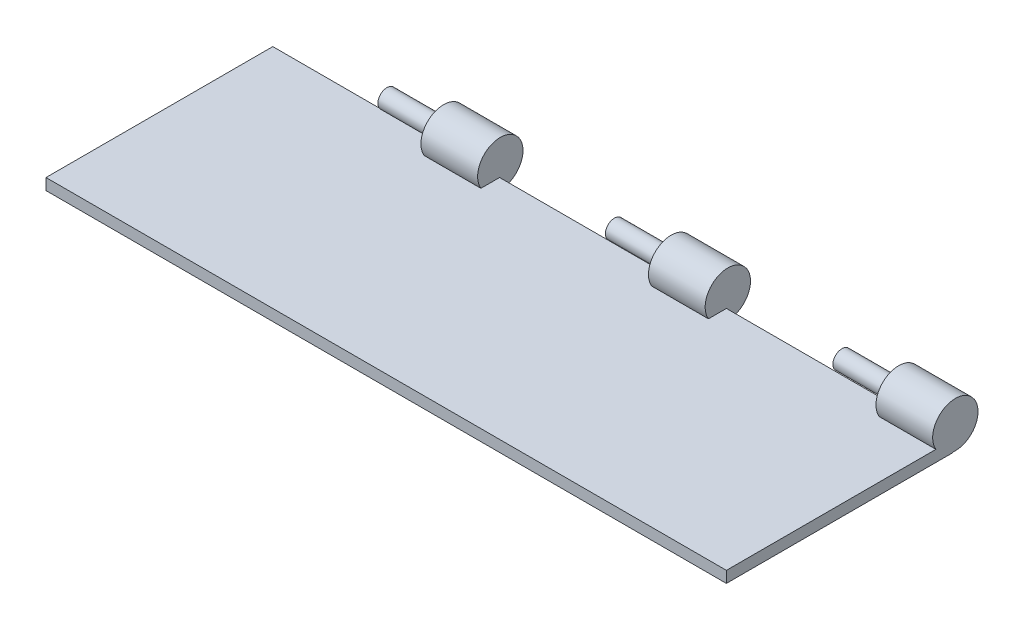
SolidWorks part; units mm, degrees
ref_plane "Front Plane" through (0, 0, 0) normal (0, 0, 1) x (1, 0, 0)
ref_plane "Top Plane" through (0, 0, 0) normal (0, 1, 0) x (1, 0, 0)
ref_plane "Right Plane" through (0, 0, 0) normal (1, 0, 0) x (0, 0, -1)
sketch "Sketch1" plane through (0, 0, 0) normal (0, 1, 0) x (1, 0, 0)
  line L1 (150, 50) -> (-150, 50)
  line L2 (150, 50) -> (150, -50)
  line L3 (150, -50) -> (-150, -50)
  line L4 (-150, 50) -> (-150, -50)
  line L5 (150, 50) -> (-150, -50) construction
  line L6 (150, -50) -> (-150, 50) construction
  point P0 (0, 0)
  dimension "D1" = 300
  dimension "D2" = 100
extrude "Boss-Extrude1" add sketch "Sketch1" along normal blind 5
ref_plane "Plane1" through (150, 0, 0) normal (1, 0, 0) x (0, 0, -1)
sketch "Sketch7" plane through (150, 0, 0) normal (1, 0, 0) x (0, 0, -1)
  circle A0 centre (50.9542, 10.1723) radius 10
  point P2 (0, 0)
  point P3 (50.9542, 10.1723)
extrude "Boss-Extrude5" add sketch "Sketch7" against normal blind 25 contours A0
sketch "Sketch10" plane through (150, 0, 0) normal (1, 0, 0) x (0, 0, -1)
  circle A0 centre (50.9542, 10.1723) radius 4
extrude "Boss-Extrude6" add sketch "Sketch10" against normal blind 50
sketch "Sketch11" plane through (0, 5, 0) normal (0, 1, 0) x (1, 0, 0)
  line L0 (150, 50.9542) -> (-150, 50) construction
  line L1 (150, 40.9542) -> (150, 60.9542) construction
pattern_linear "LPattern1" count 3 spacing 100 along (-1, 0, 0.0032) of "Boss-Extrude5", "Boss-Extrude6"
